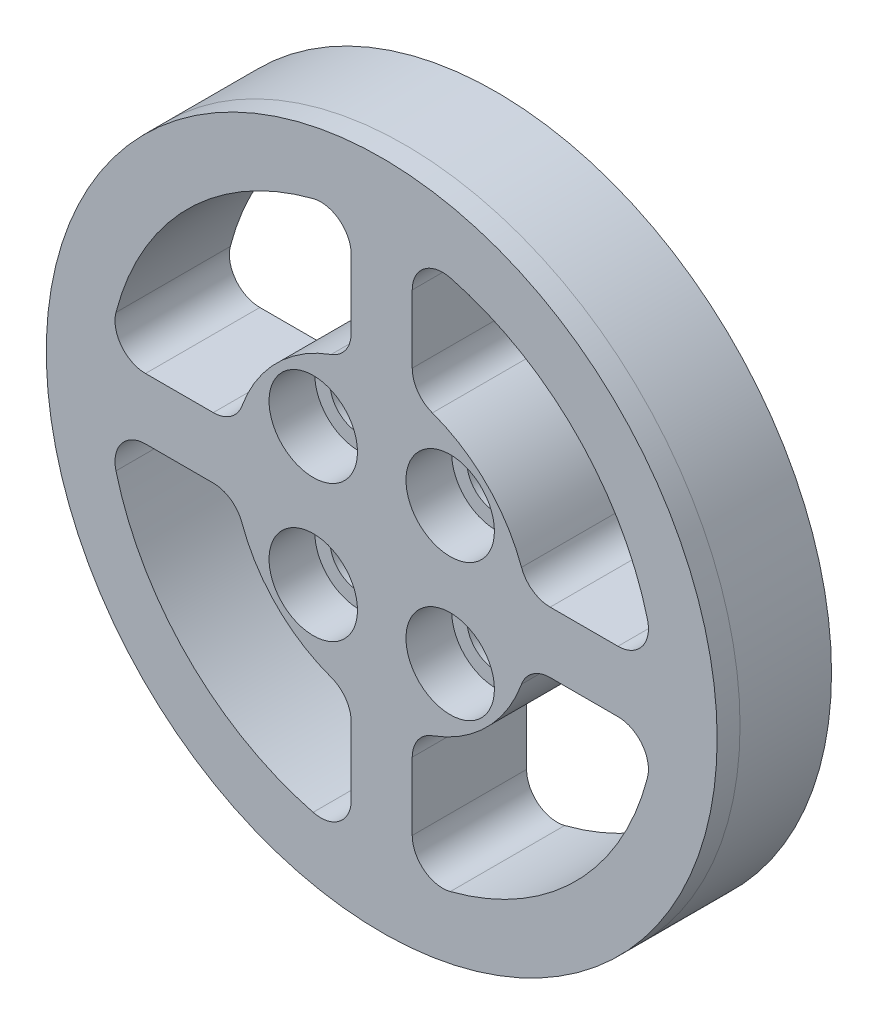
SolidWorks part; units mm, degrees
ref_plane "Front Plane" through (0, 0, 0) normal (0, 0, 1) x (1, 0, 0)
ref_plane "Top Plane" through (0, 0, 0) normal (0, 1, 0) x (1, 0, 0)
ref_plane "Right Plane" through (0, 0, 0) normal (1, 0, 0) x (0, 0, -1)
sketch "Sketch1" plane through (0, 0, 0) normal (0, 0, 1) x (1, 0, 0)
  line L0 (11.0482, 2) -> (15.4919, 2) construction
  line L1 (2, 15.4919) -> (2, 11.0482) construction
  line L2 (-15.4919, 2) -> (-11.0482, 2) construction
  line L3 (-2, 15.4919) -> (-2, 11.0482) construction
  line L4 (11.0482, 2) -> (15.4919, 2)
  line L5 (2, 15.4919) -> (2, 11.0482)
  line L6 (-15.4919, 2) -> (-11.0482, 2)
  line L7 (-2, 15.4919) -> (-2, 11.0482)
  line L8 (2, -11.0482) -> (2, -15.4919) construction
  line L9 (11.0482, -2) -> (15.4919, -2) construction
  line L10 (2, -11.0482) -> (2, -15.4919)
  line L11 (11.0482, -2) -> (15.4919, -2)
  line L12 (-15.4919, -2) -> (-11.0482, -2) construction
  line L13 (-2, -11.0482) -> (-2, -15.4919) construction
  line L14 (-15.4919, -2) -> (-11.0482, -2)
  line L15 (-2, -11.0482) -> (-2, -15.4919)
  circle A0 centre (0, 0) radius 22 construction
  circle A1 centre (0, 0) radius 22
  arc A2 (2, 11.0482) -> (3.3191, 9.1676) centre (4, 11.0482) ccw construction
  arc A3 (9.1676, 3.3191) -> (3.3191, 9.1676) centre (0, 0) ccw construction
  arc A4 (9.1676, 3.3191) -> (11.0482, 2) centre (11.0482, 4) ccw construction
  arc A5 (15.4919, 2) -> (17.4284, 4.5) centre (15.4919, 4) ccw construction
  arc A6 (17.4284, 4.5) -> (4.5, 17.4284) centre (0, 0) ccw construction
  arc A7 (4.5, 17.4284) -> (2, 15.4919) centre (4, 15.4919) ccw construction
  arc A8 (-17.4284, 4.5) -> (-15.4919, 2) centre (-15.4919, 4) ccw construction
  arc A9 (-11.0482, 2) -> (-9.1676, 3.3191) centre (-11.0482, 4) ccw construction
  arc A10 (-3.3191, 9.1676) -> (-9.1676, 3.3191) centre (0, 0) ccw construction
  arc A11 (-3.3191, 9.1676) -> (-2, 11.0482) centre (-4, 11.0482) ccw construction
  arc A12 (-2, 15.4919) -> (-4.5, 17.4284) centre (-4, 15.4919) ccw construction
  arc A13 (-4.5, 17.4284) -> (-17.4284, 4.5) centre (0, 0) ccw construction
  arc A14 (2, 11.0482) -> (3.3191, 9.1676) centre (4, 11.0482) ccw
  arc A15 (9.1676, 3.3191) -> (3.3191, 9.1676) centre (0, 0) ccw
  arc A16 (9.1676, 3.3191) -> (11.0482, 2) centre (11.0482, 4) ccw
  arc A17 (15.4919, 2) -> (17.4284, 4.5) centre (15.4919, 4) ccw
  arc A18 (17.4284, 4.5) -> (4.5, 17.4284) centre (0, 0) ccw
  arc A19 (4.5, 17.4284) -> (2, 15.4919) centre (4, 15.4919) ccw
  arc A20 (-17.4284, 4.5) -> (-15.4919, 2) centre (-15.4919, 4) ccw
  arc A21 (-11.0482, 2) -> (-9.1676, 3.3191) centre (-11.0482, 4) ccw
  arc A22 (-3.3191, 9.1676) -> (-9.1676, 3.3191) centre (0, 0) ccw
  arc A23 (-3.3191, 9.1676) -> (-2, 11.0482) centre (-4, 11.0482) ccw
  arc A24 (-2, 15.4919) -> (-4.5, 17.4284) centre (-4, 15.4919) ccw
  arc A25 (-4.5, 17.4284) -> (-17.4284, 4.5) centre (0, 0) ccw
  arc A26 (2, -15.4919) -> (4.5, -17.4284) centre (4, -15.4919) ccw construction
  arc A27 (3.3191, -9.1676) -> (2, -11.0482) centre (4, -11.0482) ccw construction
  arc A28 (3.3191, -9.1676) -> (9.1676, -3.3191) centre (0, 0) ccw construction
  arc A29 (11.0482, -2) -> (9.1676, -3.3191) centre (11.0482, -4) ccw construction
  arc A30 (17.4284, -4.5) -> (15.4919, -2) centre (15.4919, -4) ccw construction
  arc A31 (4.5, -17.4284) -> (17.4284, -4.5) centre (0, 0) ccw construction
  arc A32 (2, -15.4919) -> (4.5, -17.4284) centre (4, -15.4919) ccw
  arc A33 (3.3191, -9.1676) -> (2, -11.0482) centre (4, -11.0482) ccw
  arc A34 (3.3191, -9.1676) -> (9.1676, -3.3191) centre (0, 0) ccw
  arc A35 (11.0482, -2) -> (9.1676, -3.3191) centre (11.0482, -4) ccw
  arc A36 (17.4284, -4.5) -> (15.4919, -2) centre (15.4919, -4) ccw
  arc A37 (4.5, -17.4284) -> (17.4284, -4.5) centre (0, 0) ccw
  arc A38 (-4.5, -17.4284) -> (-2, -15.4919) centre (-4, -15.4919) ccw construction
  arc A39 (-17.4284, -4.5) -> (-4.5, -17.4284) centre (0, 0) ccw construction
  arc A40 (-15.4919, -2) -> (-17.4284, -4.5) centre (-15.4919, -4) ccw construction
  arc A41 (-9.1676, -3.3191) -> (-11.0482, -2) centre (-11.0482, -4) ccw construction
  arc A42 (-9.1676, -3.3191) -> (-3.3191, -9.1676) centre (0, 0) ccw construction
  arc A43 (-2, -11.0482) -> (-3.3191, -9.1676) centre (-4, -11.0482) ccw construction
  arc A44 (-4.5, -17.4284) -> (-2, -15.4919) centre (-4, -15.4919) ccw
  arc A45 (-17.4284, -4.5) -> (-4.5, -17.4284) centre (0, 0) ccw
  arc A46 (-15.4919, -2) -> (-17.4284, -4.5) centre (-15.4919, -4) ccw
  arc A47 (-9.1676, -3.3191) -> (-11.0482, -2) centre (-11.0482, -4) ccw
  arc A48 (-9.1676, -3.3191) -> (-3.3191, -9.1676) centre (0, 0) ccw
  arc A49 (-2, -11.0482) -> (-3.3191, -9.1676) centre (-4, -11.0482) ccw
extrude "Boss-Extrude1" add sketch "Sketch1" along normal blind 6
sketch "Sketch2" plane through (0, 0, 6) normal (0, 0, 1) x (1, 0, 0)
  line L0 (1, 23.2273) -> (-1, 23.2273) construction
  line L1 (6.5296, 22.313) -> (4.5877, 22.7916) construction
  line L2 (11.6797, 20.102) -> (9.9088, 21.0314) construction
  line L3 (16.151, 16.7227) -> (14.654, 18.049) construction
  line L4 (19.6837, 12.3716) -> (18.5476, 14.0176) construction
  line L5 (22.0725, 7.3015) -> (21.3633, 9.1715) construction
  line L6 (23.1784, 1.807) -> (22.9374, 3.7924) construction
  line L7 (22.9374, -3.7924) -> (23.1784, -1.807) construction
  line L8 (21.3633, -9.1715) -> (22.0725, -7.3015) construction
  line L9 (18.5476, -14.0176) -> (19.6837, -12.3716) construction
  line L10 (14.654, -18.049) -> (16.151, -16.7227) construction
  line L11 (9.9088, -21.0314) -> (11.6797, -20.102) construction
  line L12 (4.5877, -22.7916) -> (6.5296, -22.313) construction
  line L13 (-1, -23.2273) -> (1, -23.2273) construction
  line L14 (-6.5296, -22.313) -> (-4.5877, -22.7916) construction
  line L15 (-11.6797, -20.102) -> (-9.9088, -21.0314) construction
  line L16 (-16.151, -16.7227) -> (-14.654, -18.049) construction
  line L17 (-19.6837, -12.3716) -> (-18.5476, -14.0176) construction
  line L18 (-22.0725, -7.3015) -> (-21.3633, -9.1715) construction
  line L19 (-23.1784, -1.807) -> (-22.9374, -3.7924) construction
  line L20 (-22.9374, 3.7924) -> (-23.1784, 1.807) construction
  line L21 (-21.3633, 9.1715) -> (-22.0725, 7.3015) construction
  line L22 (-4.5877, 22.7916) -> (-6.5296, 22.313) construction
  line L23 (-9.9088, 21.0314) -> (-11.6797, 20.102) construction
  line L24 (-14.654, 18.049) -> (-16.151, 16.7227) construction
  line L25 (-18.5476, 14.0176) -> (-19.6837, 12.3716) construction
  line L26 (-4.5877, 22.7916) -> (-6.5296, 22.313)
  line L27 (-9.9088, 21.0314) -> (-11.6797, 20.102)
  line L28 (-14.654, 18.049) -> (-16.151, 16.7227)
  line L29 (-18.5476, 14.0176) -> (-19.6837, 12.3716)
  line L30 (-21.3633, 9.1715) -> (-22.0725, 7.3015)
  line L31 (-22.9374, 3.7924) -> (-23.1784, 1.807)
  line L32 (-23.1784, -1.807) -> (-22.9374, -3.7924)
  line L33 (-22.0725, -7.3015) -> (-21.3633, -9.1715)
  line L34 (-19.6837, -12.3716) -> (-18.5476, -14.0176)
  line L35 (-16.151, -16.7227) -> (-14.654, -18.049)
  line L36 (-11.6797, -20.102) -> (-9.9088, -21.0314)
  line L37 (-6.5296, -22.313) -> (-4.5877, -22.7916)
  line L38 (-1, -23.2273) -> (1, -23.2273)
  line L39 (4.5877, -22.7916) -> (6.5296, -22.313)
  line L40 (9.9088, -21.0314) -> (11.6797, -20.102)
  line L41 (14.654, -18.049) -> (16.151, -16.7227)
  line L42 (18.5476, -14.0176) -> (19.6837, -12.3716)
  line L43 (21.3633, -9.1715) -> (22.0725, -7.3015)
  line L44 (22.9374, -3.7924) -> (23.1784, -1.807)
  line L45 (23.1784, 1.807) -> (22.9374, 3.7924)
  line L46 (22.0725, 7.3015) -> (21.3633, 9.1715)
  line L47 (19.6837, 12.3716) -> (18.5476, 14.0176)
  line L48 (16.151, 16.7227) -> (14.654, 18.049)
  line L49 (11.6797, 20.102) -> (9.9088, 21.0314)
  line L50 (6.5296, 22.313) -> (4.5877, 22.7916)
  line L51 (1, 23.2273) -> (-1, 23.2273)
  line L54 (-2, 11.0482) -> (-2, 15.4919)
  line L55 (-15.4919, 2) -> (-11.0482, 2)
  line L56 (-2, 11.0482) -> (-2, 15.4919)
  line L57 (-15.4919, 2) -> (-11.0482, 2)
  line L58 (2, 15.4919) -> (2, 11.0482)
  line L59 (11.0482, 2) -> (15.4919, 2)
  line L60 (2, 15.4919) -> (2, 11.0482)
  line L61 (11.0482, 2) -> (15.4919, 2)
  line L62 (2, -11.0482) -> (2, -15.4919)
  line L63 (15.4919, -2) -> (11.0482, -2)
  line L64 (2, -11.0482) -> (2, -15.4919)
  line L65 (15.4919, -2) -> (11.0482, -2)
  line L66 (-11.0482, -2) -> (-15.4919, -2)
  line L67 (-2, -15.4919) -> (-2, -11.0482)
  line L68 (-11.0482, -2) -> (-15.4919, -2)
  line L69 (-2, -15.4919) -> (-2, -11.0482)
  arc A4 (-6.5296, -22.313) -> (-7.8013, -20.5704) centre (-8.5259, -22.4346) ccw construction
  arc A5 (-6.5296, -22.313) -> (-7.8013, -20.5704) centre (-8.5259, -22.4346) ccw
  arc A6 (-23.1784, -1.807) -> (-22.0001, 0) centre (-24, 0.0164) ccw construction
  arc A7 (-17.4284, 4.5) -> (-15.4919, 2) centre (-15.4919, 4) ccw
  arc A8 (-4.5, 17.4284) -> (-17.4284, 4.5) centre (0, 0) ccw
  arc A9 (-2, 15.4919) -> (-4.5, 17.4284) centre (-4, 15.4919) ccw
  arc A10 (-3.3191, 9.1676) -> (-2, 11.0482) centre (-4, 11.0482) ccw
  arc A11 (-3.3191, 9.1676) -> (-9.1676, 3.3191) centre (0, 0) ccw
  arc A12 (-11.0482, 2) -> (-9.1676, 3.3191) centre (-11.0482, 4) ccw
  arc A13 (-17.4284, 4.5) -> (-15.4919, 2) centre (-15.4919, 4) ccw
  arc A14 (-4.5, 17.4284) -> (-17.4284, 4.5) centre (0, 0) ccw
  arc A15 (-2, 15.4919) -> (-4.5, 17.4284) centre (-4, 15.4919) ccw
  arc A16 (-3.3191, 9.1676) -> (-2, 11.0482) centre (-4, 11.0482) ccw
  arc A17 (-3.3191, 9.1676) -> (-9.1676, 3.3191) centre (0, 0) ccw
  arc A18 (-11.0482, 2) -> (-9.1676, 3.3191) centre (-11.0482, 4) ccw
  arc A19 (-23.1784, -1.807) -> (-22.0001, 0) centre (-24, 0.0164) ccw
  arc A20 (9.1676, 3.3191) -> (3.3191, 9.1676) centre (0, 0) ccw
  arc A21 (2, 11.0482) -> (3.3191, 9.1676) centre (4, 11.0482) ccw
  arc A22 (4.5, 17.4284) -> (2, 15.4919) centre (4, 15.4919) ccw
  arc A23 (17.4284, 4.5) -> (4.5, 17.4284) centre (0, 0) ccw
  arc A24 (15.4919, 2) -> (17.4284, 4.5) centre (15.4919, 4) ccw
  arc A25 (9.1676, 3.3191) -> (11.0482, 2) centre (11.0482, 4) ccw
  arc A26 (9.1676, 3.3191) -> (3.3191, 9.1676) centre (0, 0) ccw
  arc A27 (2, 11.0482) -> (3.3191, 9.1676) centre (4, 11.0482) ccw
  arc A28 (4.5877, -22.7916) -> (2.6518, -21.8397) centre (2.8766, -23.827) ccw construction
  arc A29 (-4.5877, 22.7916) -> (-2.6518, 21.8397) centre (-2.8766, 23.827) ccw construction
  arc A30 (-2.6518, 21.8397) -> (-1, 23.2273) centre (-2.9092, 23.823) ccw construction
  arc A31 (7.8013, 20.5704) -> (9.9088, 21.0314) centre (8.4951, 22.4462) ccw construction
  arc A32 (1, 23.2273) -> (2.6518, 21.8397) centre (2.9092, 23.823) ccw construction
  arc A33 (2.6518, 21.8397) -> (4.5877, 22.7916) centre (2.8766, 23.827) ccw construction
  arc A34 (6.5296, 22.313) -> (7.8013, 20.5704) centre (8.5259, 22.4346) ccw construction
  arc A36 (11.6797, 20.102) -> (12.4975, 18.1057) centre (13.6471, 19.7423) ccw construction
  arc A37 (12.4975, 18.1057) -> (14.654, 18.049) centre (13.62, 19.761) ccw construction
  arc A38 (16.151, 16.7227) -> (16.4673, 14.5887) centre (17.9752, 15.9026) ccw construction
  arc A39 (16.4673, 14.5887) -> (18.5476, 14.0176) centre (17.9533, 15.9272) ccw construction
  arc A40 (19.6837, 12.3716) -> (19.4801, 10.2239) centre (21.2586, 11.1388) ccw construction
  arc A41 (19.4801, 10.2239) -> (21.3633, 9.1715) centre (21.2433, 11.1679) ccw construction
  arc A42 (22.0725, 7.3015) -> (21.3608, 5.265) centre (23.3065, 5.7276) ccw construction
  arc A43 (21.3608, 5.265) -> (22.9374, 3.7924) centre (23.2987, 5.7595) ccw construction
  arc A44 (23.1784, 1.807) -> (22.0001, 0) centre (24, -0.0164) ccw construction
  arc A45 (22.0001, 0) -> (23.1784, -1.807) centre (24, 0.0164) ccw construction
  arc A46 (22.9374, -3.7924) -> (21.3608, -5.265) centre (23.2987, -5.7595) ccw construction
  arc A47 (21.3608, -5.265) -> (22.0725, -7.3015) centre (23.3065, -5.7276) ccw construction
  arc A48 (21.3633, -9.1715) -> (19.4801, -10.2239) centre (21.2433, -11.1679) ccw construction
  arc A49 (19.4801, -10.2239) -> (19.6837, -12.3716) centre (21.2586, -11.1388) ccw construction
  arc A50 (18.5476, -14.0176) -> (16.4673, -14.5887) centre (17.9533, -15.9272) ccw construction
  arc A51 (16.4673, -14.5887) -> (16.151, -16.7227) centre (17.9752, -15.9026) ccw construction
  arc A52 (14.654, -18.049) -> (12.4975, -18.1057) centre (13.62, -19.761) ccw construction
  arc A53 (12.4975, -18.1057) -> (11.6797, -20.102) centre (13.6471, -19.7423) ccw construction
  arc A54 (9.9088, -21.0314) -> (7.8013, -20.5704) centre (8.4951, -22.4462) ccw construction
  arc A55 (7.8013, -20.5704) -> (6.5296, -22.313) centre (8.5259, -22.4346) ccw construction
  arc A56 (2.6518, -21.8397) -> (1, -23.2273) centre (2.9092, -23.823) ccw construction
  arc A57 (-1, -23.2273) -> (-2.6518, -21.8397) centre (-2.9092, -23.823) ccw construction
  arc A58 (-2.6518, -21.8397) -> (-4.5877, -22.7916) centre (-2.8766, -23.827) ccw construction
  arc A59 (-7.8013, -20.5704) -> (-9.9088, -21.0314) centre (-8.4951, -22.4462) ccw construction
  arc A60 (-11.6797, -20.102) -> (-12.4975, -18.1057) centre (-13.6471, -19.7423) ccw construction
  arc A61 (-12.4975, -18.1057) -> (-14.654, -18.049) centre (-13.62, -19.761) ccw construction
  arc A62 (-16.151, -16.7227) -> (-16.4673, -14.5887) centre (-17.9752, -15.9026) ccw construction
  arc A63 (-16.4673, -14.5887) -> (-18.5476, -14.0176) centre (-17.9533, -15.9272) ccw construction
  arc A64 (-19.6837, -12.3716) -> (-19.4801, -10.2239) centre (-21.2586, -11.1388) ccw construction
  arc A65 (-19.4801, -10.2239) -> (-21.3633, -9.1715) centre (-21.2433, -11.1679) ccw construction
  arc A66 (-22.0725, -7.3015) -> (-21.3608, -5.265) centre (-23.3065, -5.7276) ccw construction
  arc A67 (-21.3608, -5.265) -> (-22.9374, -3.7924) centre (-23.2987, -5.7595) ccw construction
  arc A68 (-21.3633, 9.1715) -> (-19.4801, 10.2239) centre (-21.2433, 11.1679) ccw construction
  arc A69 (-22.0001, 0) -> (-23.1784, 1.807) centre (-24, -0.0164) ccw construction
  arc A70 (-22.9374, 3.7924) -> (-21.3608, 5.265) centre (-23.2987, 5.7595) ccw construction
  arc A71 (-21.3608, 5.265) -> (-22.0725, 7.3015) centre (-23.3065, 5.7276) ccw construction
  arc A72 (-7.8013, 20.5704) -> (-6.5296, 22.313) centre (-8.5259, 22.4346) ccw construction
  arc A73 (-9.9088, 21.0314) -> (-7.8013, 20.5704) centre (-8.4951, 22.4462) ccw construction
  arc A74 (-12.4975, 18.1057) -> (-11.6797, 20.102) centre (-13.6471, 19.7423) ccw construction
  arc A75 (-14.654, 18.049) -> (-12.4975, 18.1057) centre (-13.62, 19.761) ccw construction
  arc A76 (-16.4673, 14.5887) -> (-16.151, 16.7227) centre (-17.9752, 15.9026) ccw construction
  arc A77 (-18.5476, 14.0176) -> (-16.4673, 14.5887) centre (-17.9533, 15.9272) ccw construction
  arc A78 (-19.4801, 10.2239) -> (-19.6837, 12.3716) centre (-21.2586, 11.1388) ccw construction
  arc A79 (-4.5877, 22.7916) -> (-2.6518, 21.8397) centre (-2.8766, 23.827) ccw
  arc A80 (-7.8013, 20.5704) -> (-6.5296, 22.313) centre (-8.5259, 22.4346) ccw
  arc A81 (-9.9088, 21.0314) -> (-7.8013, 20.5704) centre (-8.4951, 22.4462) ccw
  arc A82 (-12.4975, 18.1057) -> (-11.6797, 20.102) centre (-13.6471, 19.7423) ccw
  arc A83 (-14.654, 18.049) -> (-12.4975, 18.1057) centre (-13.62, 19.761) ccw
  arc A84 (-16.4673, 14.5887) -> (-16.151, 16.7227) centre (-17.9752, 15.9026) ccw
  arc A85 (-18.5476, 14.0176) -> (-16.4673, 14.5887) centre (-17.9533, 15.9272) ccw
  arc A86 (-19.4801, 10.2239) -> (-19.6837, 12.3716) centre (-21.2586, 11.1388) ccw
  arc A87 (-21.3633, 9.1715) -> (-19.4801, 10.2239) centre (-21.2433, 11.1679) ccw
  arc A88 (-21.3608, 5.265) -> (-22.0725, 7.3015) centre (-23.3065, 5.7276) ccw
  arc A89 (-22.9374, 3.7924) -> (-21.3608, 5.265) centre (-23.2987, 5.7595) ccw
  arc A90 (-22.0001, 0) -> (-23.1784, 1.807) centre (-24, -0.0164) ccw
  arc A91 (-21.3608, -5.265) -> (-22.9374, -3.7924) centre (-23.2987, -5.7595) ccw
  arc A92 (-22.0725, -7.3015) -> (-21.3608, -5.265) centre (-23.3065, -5.7276) ccw
  arc A93 (-19.4801, -10.2239) -> (-21.3633, -9.1715) centre (-21.2433, -11.1679) ccw
  arc A94 (-19.6837, -12.3716) -> (-19.4801, -10.2239) centre (-21.2586, -11.1388) ccw
  arc A95 (-16.4673, -14.5887) -> (-18.5476, -14.0176) centre (-17.9533, -15.9272) ccw
  arc A96 (-16.151, -16.7227) -> (-16.4673, -14.5887) centre (-17.9752, -15.9026) ccw
  arc A97 (-12.4975, -18.1057) -> (-14.654, -18.049) centre (-13.62, -19.761) ccw
  arc A98 (-11.6797, -20.102) -> (-12.4975, -18.1057) centre (-13.6471, -19.7423) ccw
  arc A99 (-7.8013, -20.5704) -> (-9.9088, -21.0314) centre (-8.4951, -22.4462) ccw
  arc A100 (-2.6518, -21.8397) -> (-4.5877, -22.7916) centre (-2.8766, -23.827) ccw
  arc A101 (-1, -23.2273) -> (-2.6518, -21.8397) centre (-2.9092, -23.823) ccw
  arc A102 (2.6518, -21.8397) -> (1, -23.2273) centre (2.9092, -23.823) ccw
  arc A103 (4.5877, -22.7916) -> (2.6518, -21.8397) centre (2.8766, -23.827) ccw
  arc A104 (7.8013, -20.5704) -> (6.5296, -22.313) centre (8.5259, -22.4346) ccw
  arc A105 (9.9088, -21.0314) -> (7.8013, -20.5704) centre (8.4951, -22.4462) ccw
  arc A106 (12.4975, -18.1057) -> (11.6797, -20.102) centre (13.6471, -19.7423) ccw
  arc A107 (14.654, -18.049) -> (12.4975, -18.1057) centre (13.62, -19.761) ccw
  arc A108 (16.4673, -14.5887) -> (16.151, -16.7227) centre (17.9752, -15.9026) ccw
  arc A109 (18.5476, -14.0176) -> (16.4673, -14.5887) centre (17.9533, -15.9272) ccw
  arc A110 (19.4801, -10.2239) -> (19.6837, -12.3716) centre (21.2586, -11.1388) ccw
  arc A111 (21.3633, -9.1715) -> (19.4801, -10.2239) centre (21.2433, -11.1679) ccw
  arc A112 (21.3608, -5.265) -> (22.0725, -7.3015) centre (23.3065, -5.7276) ccw
  arc A113 (22.9374, -3.7924) -> (21.3608, -5.265) centre (23.2987, -5.7595) ccw
  arc A114 (22.0001, 0) -> (23.1784, -1.807) centre (24, 0.0164) ccw
  arc A115 (23.1784, 1.807) -> (22.0001, 0) centre (24, -0.0164) ccw
  arc A116 (21.3608, 5.265) -> (22.9374, 3.7924) centre (23.2987, 5.7595) ccw
  arc A117 (22.0725, 7.3015) -> (21.3608, 5.265) centre (23.3065, 5.7276) ccw
  arc A118 (19.4801, 10.2239) -> (21.3633, 9.1715) centre (21.2433, 11.1679) ccw
  arc A119 (19.6837, 12.3716) -> (19.4801, 10.2239) centre (21.2586, 11.1388) ccw
  arc A120 (16.4673, 14.5887) -> (18.5476, 14.0176) centre (17.9533, 15.9272) ccw
  arc A121 (16.151, 16.7227) -> (16.4673, 14.5887) centre (17.9752, 15.9026) ccw
  arc A122 (12.4975, 18.1057) -> (14.654, 18.049) centre (13.62, 19.761) ccw
  arc A123 (11.6797, 20.102) -> (12.4975, 18.1057) centre (13.6471, 19.7423) ccw
  arc A124 (7.8013, 20.5704) -> (9.9088, 21.0314) centre (8.4951, 22.4462) ccw
  arc A125 (6.5296, 22.313) -> (7.8013, 20.5704) centre (8.5259, 22.4346) ccw
  arc A126 (2.6518, 21.8397) -> (4.5877, 22.7916) centre (2.8766, 23.827) ccw
  arc A127 (1, 23.2273) -> (2.6518, 21.8397) centre (2.9092, 23.823) ccw
  arc A128 (-2.6518, 21.8397) -> (-1, 23.2273) centre (-2.9092, 23.823) ccw
  arc A129 (4.5, 17.4284) -> (2, 15.4919) centre (4, 15.4919) ccw
  arc A130 (17.4284, 4.5) -> (4.5, 17.4284) centre (0, 0) ccw
  arc A131 (15.4919, 2) -> (17.4284, 4.5) centre (15.4919, 4) ccw
  arc A132 (9.1676, 3.3191) -> (11.0482, 2) centre (11.0482, 4) ccw
  arc A134 (4.5, -17.4284) -> (17.4284, -4.5) centre (0, 0) ccw
  arc A135 (2, -15.4919) -> (4.5, -17.4284) centre (4, -15.4919) ccw
  arc A136 (3.3191, -9.1676) -> (2, -11.0482) centre (4, -11.0482) ccw
  arc A137 (3.3191, -9.1676) -> (9.1676, -3.3191) centre (0, 0) ccw
  arc A138 (11.0482, -2) -> (9.1676, -3.3191) centre (11.0482, -4) ccw
  arc A139 (17.4284, -4.5) -> (15.4919, -2) centre (15.4919, -4) ccw
  arc A140 (4.5, -17.4284) -> (17.4284, -4.5) centre (0, 0) ccw
  arc A141 (2, -15.4919) -> (4.5, -17.4284) centre (4, -15.4919) ccw
  arc A142 (3.3191, -9.1676) -> (2, -11.0482) centre (4, -11.0482) ccw
  arc A143 (3.3191, -9.1676) -> (9.1676, -3.3191) centre (0, 0) ccw
  arc A144 (11.0482, -2) -> (9.1676, -3.3191) centre (11.0482, -4) ccw
  arc A145 (17.4284, -4.5) -> (15.4919, -2) centre (15.4919, -4) ccw
  arc A147 (-4.5, -17.4284) -> (-2, -15.4919) centre (-4, -15.4919) ccw
  arc A148 (-17.4284, -4.5) -> (-4.5, -17.4284) centre (0, 0) ccw
  arc A149 (-15.4919, -2) -> (-17.4284, -4.5) centre (-15.4919, -4) ccw
  arc A150 (-9.1676, -3.3191) -> (-11.0482, -2) centre (-11.0482, -4) ccw
  arc A151 (-9.1676, -3.3191) -> (-3.3191, -9.1676) centre (0, 0) ccw
  arc A152 (-2, -11.0482) -> (-3.3191, -9.1676) centre (-4, -11.0482) ccw
  arc A153 (-4.5, -17.4284) -> (-2, -15.4919) centre (-4, -15.4919) ccw
  arc A154 (-17.4284, -4.5) -> (-4.5, -17.4284) centre (0, 0) ccw
  arc A155 (-15.4919, -2) -> (-17.4284, -4.5) centre (-15.4919, -4) ccw
  arc A156 (-9.1676, -3.3191) -> (-11.0482, -2) centre (-11.0482, -4) ccw
  arc A157 (-9.1676, -3.3191) -> (-3.3191, -9.1676) centre (0, 0) ccw
  arc A158 (-2, -11.0482) -> (-3.3191, -9.1676) centre (-4, -11.0482) ccw
  dimension "D1" = 0
  dimension "D2" = 0
  dimension "D3" = 0
  dimension "D4" = 0
extrude "Boss-Extrude2" add sketch "Sketch2" along normal blind 1.5
sketch "Sketch3" plane through (0, 0, 0) normal (0, 0, -1) x (-1, 0, 0)
  circle A0 centre (0, 8) radius 1.5
  circle A1 centre (0, 8) radius 1.5 construction
  circle A2 centre (8, 0) radius 1.5
  circle A3 centre (8, 0) radius 1.5 construction
  circle A4 centre (0, -8) radius 1.5
  circle A5 centre (0, -8) radius 1.5 construction
  circle A6 centre (-8, 0) radius 1.5
  circle A7 centre (-8, 0) radius 1.5 construction
  circle A8 centre (8, 0) radius 1.375
  circle A9 centre (0, -8) radius 1.375
  circle A10 centre (0, 8) radius 1.375
  circle A11 centre (-8, 0) radius 1.375
  dimension "D1" = 0.125
extrude "Boss-Extrude3" add sketch "Sketch3" along normal blind 2.5 contours A8 | A10 | A11 | A9
sketch "Sketch4" [suppressed] plane through (0, 0, 7.5) normal (0, 0, 1) x (1, 0, 0)
  circle A0 centre (0, 0) radius 2.15
  dimension "D1" = 4.3
extrude "Cut-Extrude1" [suppressed] cut sketch "Sketch4" against normal up to next
sketch "Sketch5" [suppressed] plane through (0, 0, 7.5) normal (0, 0, 1) x (1, 0, 0)
  circle A0 centre (0, 0) radius 5.25
  dimension "D1" = 10.5
extrude "Cut-Extrude2" [suppressed] cut sketch "Sketch5" against normal offset from surface (5.5 mm away) 2
sketch "Sketch6" plane through (0, 0, 7.5) normal (0, 0, 1) x (1, 0, 0)
  line L0 (0, 0) -> (6.8943, 6.8943) construction
  line L1 (0, 6.35) -> (0, -6.35) construction
  line L2 (-6.35, 0) -> (6.35, 0) construction
  circle A0 centre (0, 0) radius 6.35
  arc A1 (9.1676, 3.3191) -> (3.3191, 9.1676) centre (0, 0) ccw construction
  circle A2 centre (4.4901, 4.4901) radius 1.9
  circle A3 centre (-4.4901, 4.4901) radius 1.9
  circle A4 centre (4.4901, -4.4901) radius 1.9
  circle A5 centre (-4.4901, -4.4901) radius 1.9
  dimension "D1" = 12.7
  dimension "D2" = 3.8
extrude "Cut-Extrude3" cut sketch "Sketch6" against normal up to next contours A3 A0 | A3 A0 | A0 A2 | A0 A2 | A4 A0 | A4 A0 | A0 A5 | A0 A5
sketch "Sketch7" plane through (0, 0, 7.5) normal (0, 0, 1) x (1, 0, 0)
  circle A0 centre (-4.4901, 4.4901) radius 2.9
  circle A1 centre (4.4901, 4.4901) radius 2.9
  circle A2 centre (4.4901, -4.4901) radius 2.9
  circle A3 centre (-4.4901, -4.4901) radius 2.9
  dimension "D1" = 5.8
extrude "Cut-Extrude4" cut sketch "Sketch7" against normal blind 3
sketch "Sketch8" plane through (0, 0, 7.5) normal (0, 0, 1) x (1, 0, 0)
  circle A0 centre (0, 0) radius 23.2488
  circle A1 centre (0, 0) radius 22.0001
extrude "Cut-Extrude5" cut sketch "Sketch8" against normal up to next
